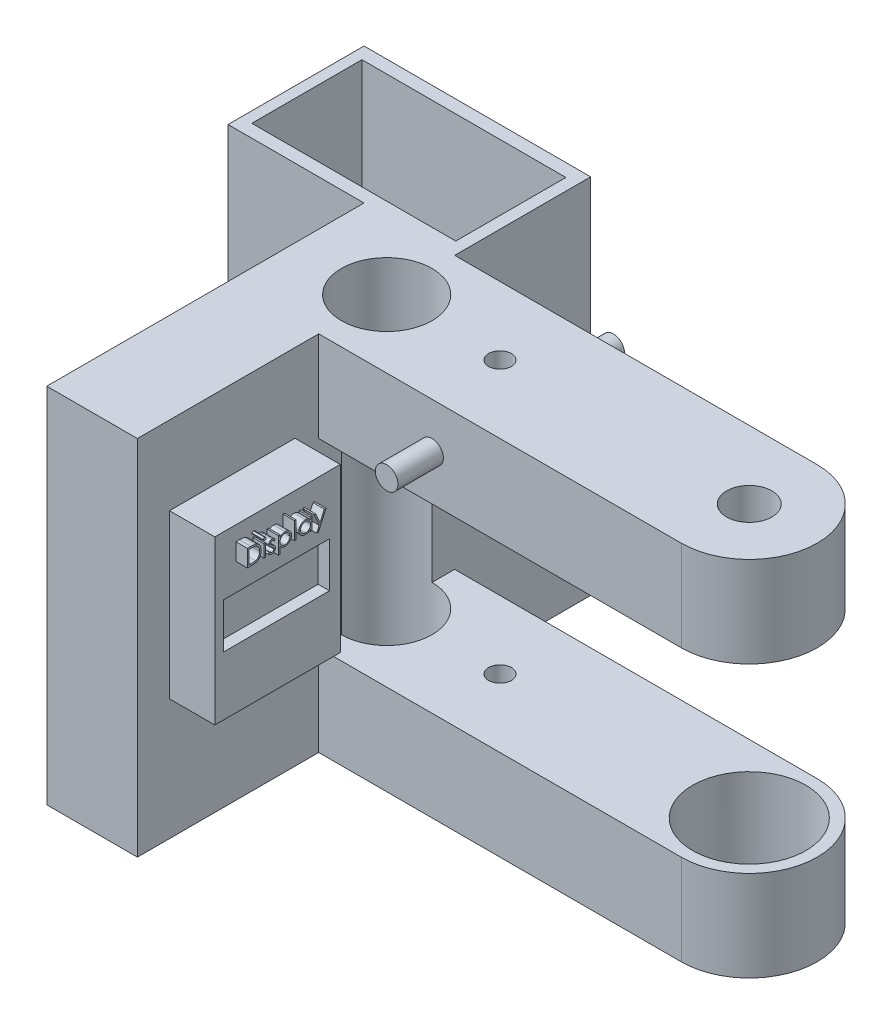
SolidWorks part; units mm, degrees
ref_plane "Front Plane" through (0, 0, 0) normal (0, 0, 1) x (1, 0, 0)
ref_plane "Top Plane" through (0, 0, 0) normal (0, 1, 0) x (1, 0, 0)
ref_plane "Right Plane" through (0, 0, 0) normal (1, 0, 0) x (0, 0, -1)
sketch "Sketch2" plane through (0, 0, 0) normal (0, 1, 0) x (1, 0, 0)
  line L0 (0, 38.1) -> (0, -38.1)
  line L1 (-254, 38.1) -> (254, 38.1)
  line L2 (-254, 38.1) -> (-254, -38.1)
  line L3 (-254, -38.1) -> (254, -38.1)
  line L4 (254, 38.1) -> (254, -38.1)
  line L5 (-254, 38.1) -> (254, -38.1) construction
  line L6 (-254, -38.1) -> (254, 38.1) construction
  line L7 (0, 38.1) -> (-50.8, 38.1)
  line L8 (-50.8, 38.1) -> (-50.8, -38.1)
  circle A0 centre (0, 0) radius 25.4
  dimension "D1" = 50.8
  dimension "D2" = 508
  dimension "D3" = 76.2
  dimension "D4" = 50.8
extrude "Boss-Extrude1" add sketch "Sketch2" along normal blind 50.8 contours A0 L0 L3 L4 L1 | A0 L0 L1 L8 L3
sketch "Sketch3" plane through (0, 0, 38.1) normal (0, 0, 1) x (1, 0, 0)
  line L1 (-50.8, 0) -> (0, 0)
  line L2 (-50.8, 0) -> (-50.8, -152.4)
  line L3 (-50.8, -152.4) -> (0, -152.4)
  line L4 (0, 0) -> (0, -152.4)
  dimension "D1" = 152.4
extrude "Boss-Extrude2" add sketch "Sketch3" against normal blind 76.2
sketch "Sketch4" plane through (0, 0, 0) normal (1, 0, 0) x (0, 0, -1)
  line L0 (38.1, -152.4) -> (38.1, 0) construction
  line L1 (-38.1, -152.4) -> (38.1, -152.4)
  line L2 (-38.1, -152.4) -> (-38.1, -101.6)
  line L3 (-38.1, -101.6) -> (38.1, -101.6)
  line L4 (38.1, -152.4) -> (38.1, -101.6)
  dimension "D1" = 50.8
extrude "Boss-Extrude3" add sketch "Sketch4" along normal blind 254
sketch "Sketch5" plane through (0, 50.8, 0) normal (0, 1, 0) x (1, 0, 0)
  line L0 (254, 38.1) -> (203.2, 38.1)
  line L1 (-50.8, 38.1) -> (254, 38.1) construction
  line L2 (203.2, 38.1) -> (203.2, -38.1)
  line L3 (-50.8, -38.1) -> (254, -38.1) construction
  circle A0 centre (203.2, 0) radius 12.7
  dimension "D2" = 25.4
  dimension "D1" = 50.8
extrude "Cut-Extrude1" cut sketch "Sketch5" against normal up to surface (152.4 mm away) contours A0 up to face at (127, -101.6, 0)
sketch "Sketch6" plane through (0, -101.6, 0) normal (0, 1, 0) x (1, 0, 0)
  circle A0 centre (203.2, 0) radius 31.75
  dimension "D1" = 63.5
extrude "Cut-Extrude2" cut sketch "Sketch6" against normal blind 254
sketch "Sketch8" plane through (0, 50.8, 0) normal (0, 1, 0) x (1, 0, 0)
  circle A0 centre (0, 0) radius 25.4
extrude "Cut-Extrude3" cut sketch "Sketch8" against normal through all
sketch "Sketch9" plane through (0, 50.8, 0) normal (0, 1, 0) x (1, 0, 0)
  line L0 (-50.8, 38.1) -> (101.6, 38.1)
  line L1 (-50.8, 38.1) -> (254, 38.1) construction
  line L2 (25.4, 38.1) -> (101.6, 38.1)
  line L3 (63.5, 38.1) -> (63.5, -38.1)
  line L4 (-50.8, -38.1) -> (254, -38.1) construction
  circle A0 centre (63.5, 0) radius 6.35
  dimension "D1" = 12.7
extrude "Cut-Extrude5" cut sketch "Sketch9" against normal through all contours A0
sketch "Sketch10" plane through (0, 50.8, 0) normal (0, 1, 0) x (1, 0, 0)
  circle A0 centre (63.5, 0) radius 6.5093
sketch "Sketch11" plane through (0, 0, 38.1) normal (0, 0, 1) x (1, 0, 0)
  line L0 (57.15, 25.4) -> (-50.8, 25.4)
  line L1 (57.15, 50.8) -> (57.15, 0) construction
  line L2 (-50.8, 50.8) -> (-50.8, -152.4) construction
  line L3 (57.15, 25.4) -> (69.85, 25.4)
  line L4 (69.85, 0) -> (69.85, 50.8) construction
  circle A0 centre (63.5, 25.4) radius 6.35
  dimension "D1" = 12.7
extrude "Boss-Extrude5" add sketch "Sketch11" along normal blind 25.4 contours L3 A0 | L3 A0
sketch "Sketch12" plane through (0, 0, -38.1) normal (0, 0, -1) x (-1, 0, 0)
  line L0 (-57.15, 25.4) -> (-69.85, 25.4)
  line L1 (-57.15, 0) -> (-57.15, 50.8) construction
  line L2 (-69.85, 50.8) -> (-69.85, 0) construction
  circle A0 centre (-63.5, 25.4) radius 6.35
extrude "Boss-Extrude6" add sketch "Sketch12" along normal blind 25.4 contours L0 A0 | L0 A0
sketch "Sketch14" plane through (0, 0, 38.1) normal (0, 0, 1) x (1, 0, 0)
  line L0 (-50.8, -152.4) -> (254, -152.4) construction
  line L1 (-50.8, 50.8) -> (0, 50.8)
  line L2 (-50.8, 50.8) -> (-50.8, -152.4)
  line L3 (-50.8, -152.4) -> (0, -152.4)
  line L4 (0, 50.8) -> (0, -152.4)
extrude "Boss-Extrude7" add sketch "Sketch14" along normal blind 101.6
sketch "Sketch15" plane through (0, 0, 0) normal (1, 0, 0) x (0, 0, -1)
  line L1 (-121.7259, 6.7604) -> (-51.4037, 6.7604)
  line L2 (-121.7259, 6.7604) -> (-121.7259, -84.5349)
  line L3 (-121.7259, -84.5349) -> (-51.4037, -84.5349)
  line L4 (-51.4037, 6.7604) -> (-51.4037, -84.5349)
  line L5 (-121.7259, 6.7604) -> (-51.4037, -84.5349) construction
  line L6 (-121.7259, -84.5349) -> (-51.4037, 6.7604) construction
  point P0 (-86.5648, -38.8873)
extrude "Boss-Extrude8" add sketch "Sketch15" along normal blind 25.4
sketch "Sketch16" plane through (25.4, 0, 0) normal (1, 0, 0) x (0, 0, -1)
  text T0 "Display" font "Century Gothic" height in points 36
extrude "Boss-Extrude9" add sketch "Sketch16" along normal blind 6.35
sketch "Sketch17" plane through (25.4, 0, 0) normal (1, 0, 0) x (0, 0, -1)
  line L1 (-116.7168, -26.2377) -> (-57.4581, -26.2377)
  line L2 (-116.7168, -26.2377) -> (-116.7168, -51.5368)
  line L3 (-116.7168, -51.5368) -> (-57.4581, -51.5368)
  line L4 (-57.4581, -26.2377) -> (-57.4581, -51.5368)
  line L5 (-116.7168, -26.2377) -> (-57.4581, -51.5368) construction
  line L6 (-116.7168, -51.5368) -> (-57.4581, -26.2377) construction
  point P0 (-87.0874, -38.8873)
extrude "Cut-Extrude6" cut sketch "Sketch17" against normal blind 6.35
sketch "Sketch18" plane through (0, -152.4, 0) normal (0, -1, 0) x (1, 0, 0)
  line L1 (203.2, -38.1) -> (254, -38.1)
  line L2 (254, -38.1) -> (254, 38.1)
  line L3 (254, 38.1) -> (203.2, 38.1)
  arc A0 (203.2, -38.1) -> (203.2, 38.1) centre (203.2, 0) ccw
extrude "Cut-Extrude7" cut sketch "Sketch18" against normal through all contours L3 A0 L1 L2
sketch "Sketch19" plane through (0, 0, -38.1) normal (0, 0, -1) x (-1, 0, 0)
  line L0 (50.8, -152.4) -> (-203.2, -152.4) construction
  line L1 (50.8, 50.8) -> (0, 50.8)
  line L2 (50.8, 50.8) -> (50.8, -152.4)
  line L3 (50.8, -152.4) -> (0, -152.4)
  line L4 (0, 50.8) -> (0, -152.4)
extrude "Boss-Extrude10" add sketch "Sketch19" along normal blind 76.2
sketch "Sketch20" plane through (-50.8, 0, 0) normal (-1, 0, 0) x (0, 0, 1)
  line L1 (-114.3, 50.8) -> (-38.1, 50.8)
  line L2 (-114.3, 50.8) -> (-114.3, -152.4)
  line L3 (-114.3, -152.4) -> (-38.1, -152.4)
  line L4 (-38.1, 50.8) -> (-38.1, -152.4)
extrude "Boss-Extrude11" add sketch "Sketch20" along normal blind 76.2
sketch "Sketch21" plane through (0, 50.8, 0) normal (0, 1, 0) x (1, 0, 0)
  line L1 (-127, 114.3) -> (0, 114.3)
  line L2 (-127, 114.3) -> (-127, 38.1)
  line L3 (-127, 38.1) -> (0, 38.1)
  line L4 (0, 114.3) -> (0, 38.1)
  line L5 (-120.929, 107.0587) -> (-6.629, 107.0587)
  line L6 (-120.929, 107.0587) -> (-120.929, 45.3413)
  line L7 (-120.929, 45.3413) -> (-6.629, 45.3413)
  line L8 (-6.629, 107.0587) -> (-6.629, 45.3413)
  line L9 (-120.929, 107.0587) -> (-6.629, 45.3413) construction
  line L10 (-120.929, 45.3413) -> (-6.629, 107.0587) construction
  point P6 (-63.779, 76.2)
  dimension "D1" = 114.3
  dimension "D2" = 61.7174
extrude "Cut-Extrude9" cut sketch "Sketch21" against normal blind 190.5 contours L8 L5 L6 L7
sketch "Sketch22" plane through (0, -139.7, 0) normal (0, 1, 0) x (1, 0, 0)
  line L0 (-6.629, 76.2) -> (-120.929, 76.2)
  line L1 (-6.629, 107.0587) -> (-6.629, 45.3413) construction
  line L2 (-120.929, 107.0587) -> (-120.929, 45.3413) construction
  circle A0 centre (-63.779, 76.2) radius 6.35
  dimension "D1" = 12.7
extrude "Cut-Extrude10" cut sketch "Sketch22" against normal blind 190.5 contours L0 A0 | L0 A0
